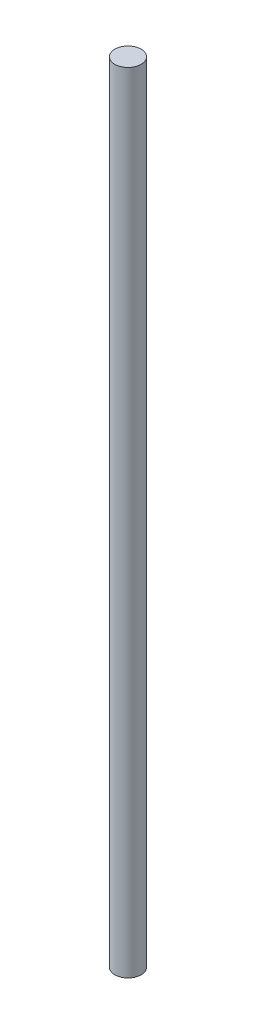
SolidWorks part; units mm, degrees
ref_plane "Front Plane" through (0, 0, 0) normal (0, 0, 1) x (1, 0, 0)
ref_plane "Top Plane" through (0, 0, 0) normal (0, 1, 0) x (1, 0, 0)
ref_plane "Right Plane" through (0, 0, 0) normal (1, 0, 0) x (0, 0, -1)
sketch "Sketch1" plane through (0, 0, 0) normal (0, 1, 0) x (1, 0, 0)
  circle A0 centre (0, 0) radius 2.5
  dimension "D1" = 5
extrude "Boss-Extrude1" add sketch "Sketch1" along normal blind 150
